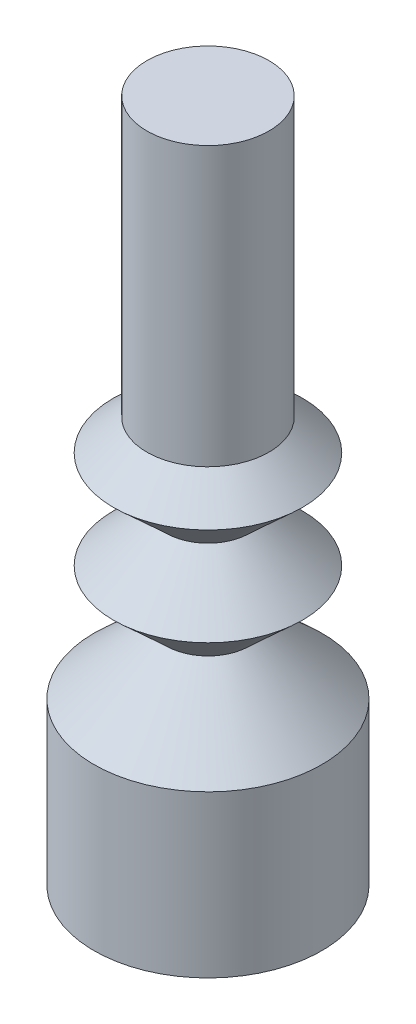
SolidWorks part; units mm, degrees
ref_plane "Front Plane" through (0, 0, 0) normal (0, 0, 1) x (1, 0, 0)
ref_plane "Top Plane" through (0, 0, 0) normal (0, 1, 0) x (1, 0, 0)
ref_plane "Right Plane" through (0, 0, 0) normal (1, 0, 0) x (0, 0, -1)
sketch "Sketch1" plane through (0, 0, 0) normal (0, 0, 1) x (1, 0, 0)
  line L0 (0, 12.5) -> (0, -12.5) construction
  line L1 (12.5, 12.5) -> (-12.5, 12.5) construction
  line L2 (-4.75, -12.5) -> (4.75, -12.5) construction
  line L3 (0, 8.5) -> (1.875, 8.5)
  line L4 (-1.875, 8.5) -> (1.875, 8.5) construction
  line L33 (1.875, 8.5) -> (1.875, 4.5)
  line L34 (0, 8.5) -> (0, -12.5)
  line L35 (0, -12.5) -> (3.5, -12.5)
  line L40 (1.875, 4.5) -> (1.875, -0.0473)
  line L41 (3.5, -7.5473) -> (3.5, -12.5)
  line L42 (1.2821, -5.5) -> (3.5, -7.5473)
  line L43 (2.9071, -4) -> (1.2821, -5.5)
  line L44 (1.2821, -2.5) -> (2.9071, -4)
  line L45 (2.9071, -1) -> (1.2821, -2.5)
  line L46 (1.875, -0.0473) -> (2.9071, -1)
  line L47 (1.875, 4.5) -> (1.875, -0.0473)
  line L48 (3.5, -7.5473) -> (3.5, -12.5)
  line L49 (1.2821, -5.5) -> (3.5, -7.5473)
  line L50 (2.9071, -4) -> (1.2821, -5.5)
  line L51 (1.2821, -2.5) -> (2.9071, -4)
  line L52 (2.9071, -1) -> (1.2821, -2.5)
  line L53 (1.875, -0.0473) -> (2.9071, -1)
  dimension "D1" = 1.25
revolve "Revolve1" add sketch "Sketch1" angle 360 about L0
